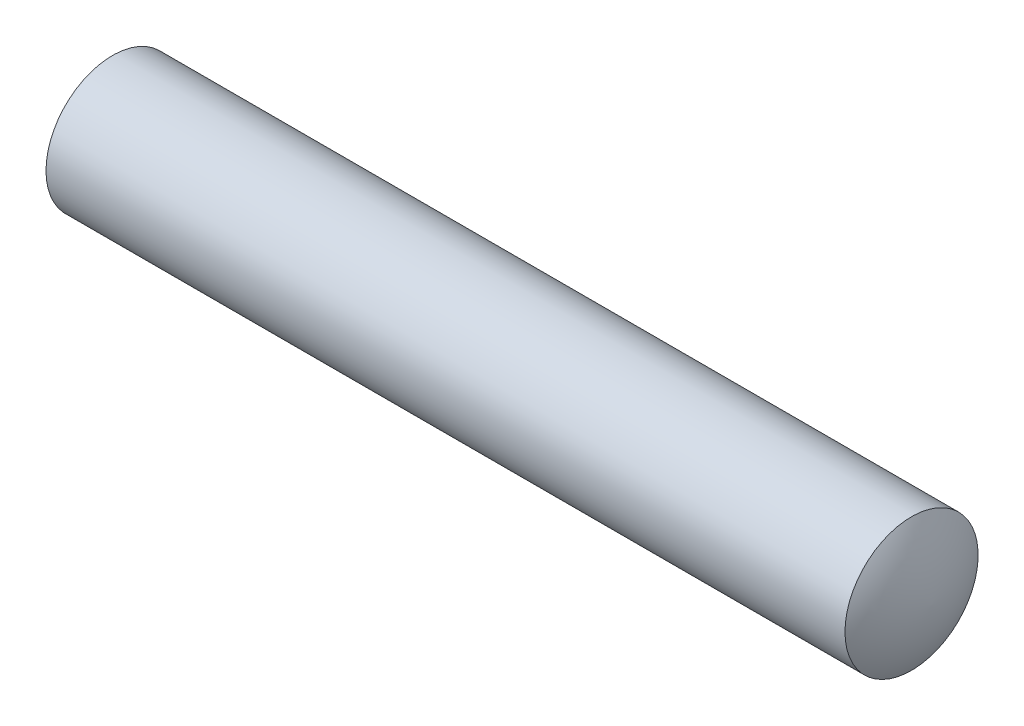
SolidWorks part; units mm, degrees
ref_plane "Спереди" through (0, 0, 0) normal (0, 0, 1) x (1, 0, 0)
ref_plane "Сверху" through (0, 0, 0) normal (0, 1, 0) x (1, 0, 0)
ref_plane "Справа" through (0, 0, 0) normal (1, 0, 0) x (0, 0, -1)
sketch "Эскиз1" plane through (0, 0, 0) normal (0, 0, 1) x (1, 0, 0)
  line L0 (0, 0) -> (14.3069, 0) construction
  line L1 (0, 0) -> (0, 6.3046) construction
  line L3 (0, 2) -> (24, 2)
  line L6 (24, 2) -> (24, -0.9836) construction
  line L7 (-0.6, 0) -> (24.6, 0)
  arc A1 (0, 2) -> (-0.6, 0) centre (3.3985, -0.1095) ccw
  arc A2 (24, 2) -> (24.6, 0) centre (20.6015, -0.1095) cw
  dimension "D1" = 0.6
  dimension "D4" = 4
  dimension "D6" = 4
  dimension "D2" = 4
  dimension "D3" = 24
  dimension "D5" = 0.6
revolve "Повернуть2" add sketch "Эскиз1" angle 360 about L0
